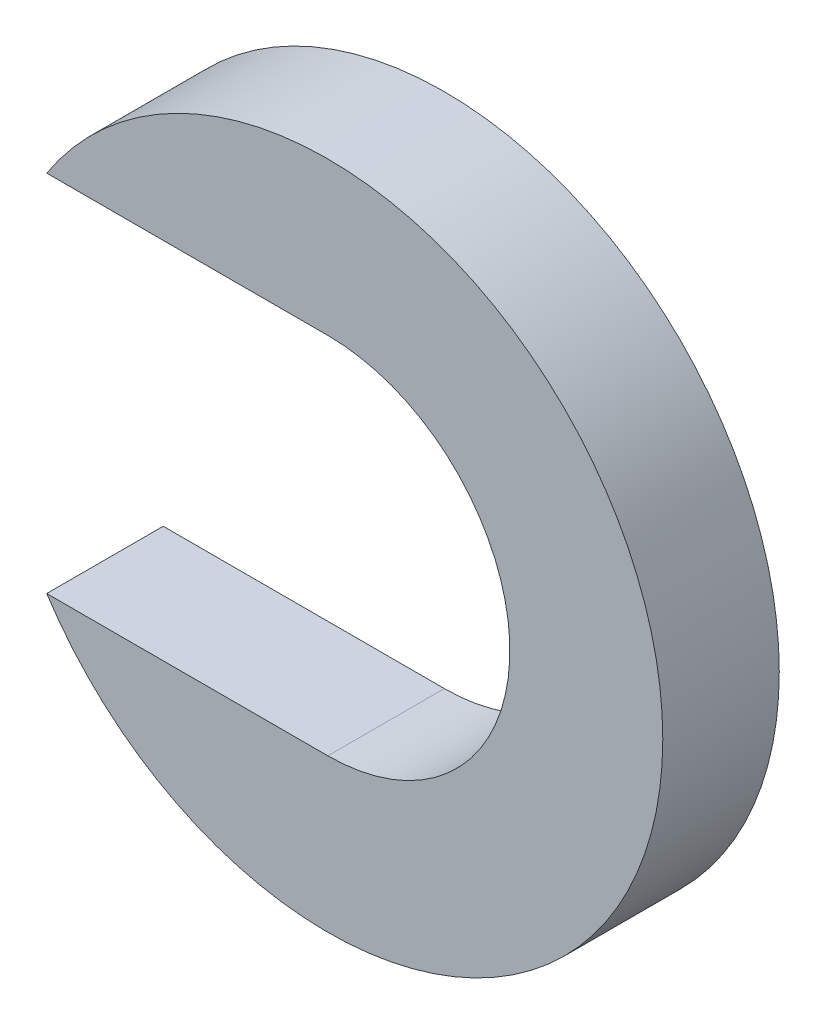
SolidWorks part; units mm, degrees
ref_plane "Front Plane" through (0, 0, 0) normal (0, 0, 1) x (1, 0, 0)
ref_plane "Top Plane" through (0, 0, 0) normal (0, 1, 0) x (1, 0, 0)
ref_plane "Right Plane" through (0, 0, 0) normal (1, 0, 0) x (0, 0, -1)
sketch "Sketch1" plane through (0, 0, 0) normal (0, 0, 1) x (1, 0, 0)
  line L0 (-7.6624, -4.9609) -> (0, -4.9609)
  line L1 (0, 4.9609) -> (-7.6624, 4.9609)
  line L2 (0, 0) -> (-13.6181, 0) construction
  arc A0 (-7.6624, -4.9609) -> (-7.6624, 4.9609) centre (0, 0) ccw
  arc A1 (0, -4.9609) -> (0, 4.9609) centre (0, 0) ccw
  dimension "D1" = 18.2562
  dimension "D2" = 9.9219
extrude "Extrude1" add sketch "Sketch1" along normal blind 3.175
